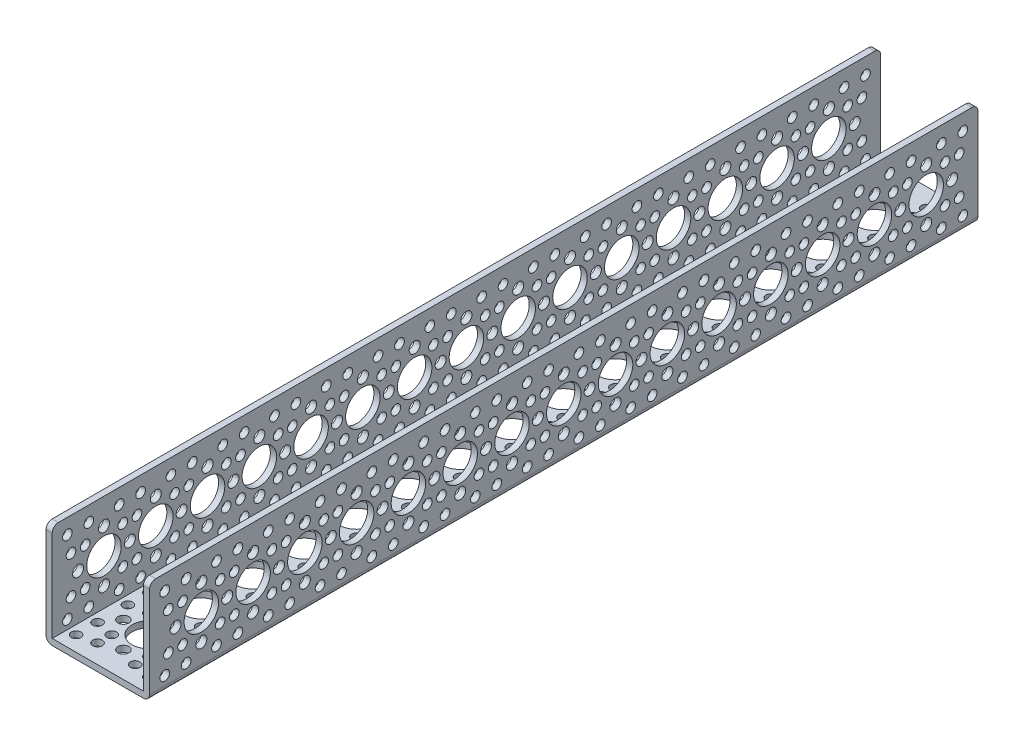
SolidWorks part; units mm, degrees
ref_plane "Front Plane" through (0, 0, 0) normal (0, 0, 1) x (1, 0, 0)
ref_plane "Top Plane" through (0, 0, 0) normal (0, 1, 0) x (1, 0, 0)
ref_plane "Right Plane" through (0, 0, 0) normal (1, 0, 0) x (0, 0, -1)
sketch "Sketch1" plane through (0, 0, 0) normal (0, 0, 1) x (1, 0, 0)
  line L1 (0, 0) -> (38.1, 0)
  line L2 (0, 0) -> (0, 38.1)
  line L4 (38.1, 0) -> (38.1, 38.1)
extrude "Extrude-Thin1" add sketch "Sketch1" along normal blind 304.8 thin thin type one direction wall 2.286
sketch "Sketch3" plane through (0, 0, 0) normal (0, -1, 0) x (1, 0, 0)
  line L0 (38.1, 0) -> (0, 0) construction
  circle B0 centre (19.05, 19.0584) radius 6.35
  circle B1 centre (19.05, 9.5334) radius 2.032
  circle B2 centre (9.525, 19.0584) radius 2.032
  circle B3 centre (19.05, 28.5834) radius 2.032
  circle B4 centre (28.575, 19.0584) radius 2.032
  circle B5 centre (12.1352, 25.9732) radius 1.778
  circle B6 centre (5.5796, 32.5288) radius 1.778
  circle B7 centre (25.9648, 25.9732) radius 1.778
  circle B8 centre (32.5204, 32.5288) radius 1.778
  circle B9 centre (25.9648, 12.1436) radius 1.778
  circle B10 centre (32.5204, 5.588) radius 1.778
  circle B11 centre (12.1352, 12.1436) radius 1.778
  circle B12 centre (5.5796, 5.588) radius 1.778
  circle B13 centre (12.1352, 31.1936) radius 1.778
  circle B14 centre (25.9648, 31.1936) radius 1.778
  circle B15 centre (25.9648, 6.9232) radius 1.778
  circle B16 centre (12.1352, 6.9232) radius 1.778
  circle B17 centre (32.5204, 13.4788) radius 1.778
  circle B18 centre (5.5796, 13.4788) radius 1.778
  circle B19 centre (5.5796, 24.638) radius 1.778
  circle B20 centre (32.5204, 24.638) radius 1.778
  circle B21 centre (18.9713, 38.1084) radius 6.35
  circle B22 centre (9.4463, 38.1084) radius 2.032
  circle B23 centre (28.4963, 38.1084) radius 2.032
  circle B24 centre (18.9713, 57.1584) radius 6.35
  circle B25 centre (18.9713, 47.6334) radius 2.032
  circle B26 centre (9.4463, 57.1584) radius 2.032
  circle B27 centre (18.9713, 66.6834) radius 2.032
  circle B28 centre (28.4963, 57.1584) radius 2.032
  circle B29 centre (12.0565, 64.0732) radius 1.778
  circle B30 centre (5.5009, 70.6288) radius 1.778
  circle B31 centre (25.8861, 64.0732) radius 1.778
  circle B32 centre (32.4417, 70.6288) radius 1.778
  circle B33 centre (25.8861, 50.2436) radius 1.778
  circle B34 centre (32.4417, 43.688) radius 1.778
  circle B35 centre (12.0565, 50.2436) radius 1.778
  circle B36 centre (5.5009, 43.688) radius 1.778
  circle B37 centre (12.0565, 69.2936) radius 1.778
  circle B38 centre (25.8861, 69.2936) radius 1.778
  circle B39 centre (25.8861, 45.0232) radius 1.778
  circle B40 centre (12.0565, 45.0232) radius 1.778
  circle B41 centre (32.4417, 51.5788) radius 1.778
  circle B42 centre (5.5009, 51.5788) radius 1.778
  circle B43 centre (5.5009, 62.738) radius 1.778
  circle B44 centre (32.4417, 62.738) radius 1.778
  circle B45 centre (18.9713, 76.2084) radius 6.35
  circle B46 centre (9.4463, 76.2084) radius 2.032
  circle B47 centre (28.4963, 76.2084) radius 2.032
  circle B48 centre (18.9713, 95.2584) radius 6.35
  circle B49 centre (18.9713, 85.7334) radius 2.032
  circle B50 centre (9.4463, 95.2584) radius 2.032
  circle B51 centre (18.9713, 104.7834) radius 2.032
  circle B52 centre (28.4963, 95.2584) radius 2.032
  circle B53 centre (12.0565, 102.1732) radius 1.778
  circle B54 centre (5.5009, 108.7288) radius 1.778
  circle B55 centre (25.8861, 102.1732) radius 1.778
  circle B56 centre (32.4417, 108.7288) radius 1.778
  circle B57 centre (25.8861, 88.3436) radius 1.778
  circle B58 centre (32.4417, 81.788) radius 1.778
  circle B59 centre (12.0565, 88.3436) radius 1.778
  circle B60 centre (5.5009, 81.788) radius 1.778
  circle B61 centre (12.0565, 107.3936) radius 1.778
  circle B62 centre (25.8861, 107.3936) radius 1.778
  circle B63 centre (25.8861, 83.1232) radius 1.778
  circle B64 centre (12.0565, 83.1232) radius 1.778
  circle B65 centre (32.4417, 89.6788) radius 1.778
  circle B66 centre (5.5009, 89.6788) radius 1.778
  circle B67 centre (5.5009, 100.838) radius 1.778
  circle B68 centre (32.4417, 100.838) radius 1.778
  circle B69 centre (18.9713, 133.3584) radius 6.35
  circle B70 centre (18.9713, 123.8334) radius 2.032
  circle B71 centre (9.4463, 133.3584) radius 2.032
  circle B72 centre (18.9713, 142.8834) radius 2.032
  circle B73 centre (28.4963, 133.3584) radius 2.032
  circle B74 centre (12.0565, 140.2732) radius 1.778
  circle B75 centre (5.5009, 146.8288) radius 1.778
  circle B76 centre (25.8861, 140.2732) radius 1.778
  circle B77 centre (32.4417, 146.8288) radius 1.778
  circle B78 centre (25.8861, 126.4436) radius 1.778
  circle B79 centre (32.4417, 119.888) radius 1.778
  circle B80 centre (12.0565, 126.4436) radius 1.778
  circle B81 centre (5.5009, 119.888) radius 1.778
  circle B82 centre (12.0565, 145.4936) radius 1.778
  circle B83 centre (25.8861, 145.4936) radius 1.778
  circle B84 centre (25.8861, 121.2232) radius 1.778
  circle B85 centre (12.0565, 121.2232) radius 1.778
  circle B86 centre (32.4417, 127.7788) radius 1.778
  circle B87 centre (5.5009, 127.7788) radius 1.778
  circle B88 centre (5.5009, 138.938) radius 1.778
  circle B89 centre (32.4417, 138.938) radius 1.778
  circle B90 centre (18.9713, 114.3084) radius 6.35
  circle B91 centre (9.4463, 114.3084) radius 2.032
  circle B92 centre (28.4963, 114.3084) radius 2.032
  circle B93 centre (18.9713, 152.4084) radius 6.35
  circle B94 centre (9.4463, 152.4084) radius 2.032
  circle B95 centre (28.4963, 152.4084) radius 2.032
  circle B96 centre (18.9713, 171.4584) radius 6.35
  circle B97 centre (18.9713, 161.9334) radius 2.032
  circle B98 centre (9.4463, 171.4584) radius 2.032
  circle B99 centre (18.9713, 180.9834) radius 2.032
  circle B100 centre (28.4963, 171.4584) radius 2.032
  circle B101 centre (12.0565, 178.3732) radius 1.778
  circle B102 centre (5.5009, 184.9288) radius 1.778
  circle B103 centre (25.8861, 178.3732) radius 1.778
  circle B104 centre (32.4417, 184.9288) radius 1.778
  circle B105 centre (25.8861, 164.5436) radius 1.778
  circle B106 centre (32.4417, 157.988) radius 1.778
  circle B107 centre (12.0565, 164.5436) radius 1.778
  circle B108 centre (5.5009, 157.988) radius 1.778
  circle B109 centre (12.0565, 183.5936) radius 1.778
  circle B110 centre (25.8861, 183.5936) radius 1.778
  circle B111 centre (25.8861, 159.3232) radius 1.778
  circle B112 centre (12.0565, 159.3232) radius 1.778
  circle B113 centre (32.4417, 165.8788) radius 1.778
  circle B114 centre (5.5009, 165.8788) radius 1.778
  circle B115 centre (5.5009, 177.038) radius 1.778
  circle B116 centre (32.4417, 177.038) radius 1.778
  circle B117 centre (18.9713, 209.5584) radius 6.35
  circle B118 centre (18.9713, 200.0334) radius 2.032
  circle B119 centre (9.4463, 209.5584) radius 2.032
  circle B120 centre (18.9713, 219.0834) radius 2.032
  circle B121 centre (28.4963, 209.5584) radius 2.032
  circle B122 centre (12.0565, 216.4732) radius 1.778
  circle B123 centre (5.5009, 223.0288) radius 1.778
  circle B124 centre (25.8861, 216.4732) radius 1.778
  circle B125 centre (32.4417, 223.0288) radius 1.778
  circle B126 centre (25.8861, 202.6436) radius 1.778
  circle B127 centre (32.4417, 196.088) radius 1.778
  circle B128 centre (12.0565, 202.6436) radius 1.778
  circle B129 centre (5.5009, 196.088) radius 1.778
  circle B130 centre (12.0565, 221.6936) radius 1.778
  circle B131 centre (25.8861, 221.6936) radius 1.778
  circle B132 centre (25.8861, 197.4232) radius 1.778
  circle B133 centre (12.0565, 197.4232) radius 1.778
  circle B134 centre (32.4417, 203.9788) radius 1.778
  circle B135 centre (5.5009, 203.9788) radius 1.778
  circle B136 centre (5.5009, 215.138) radius 1.778
  circle B137 centre (32.4417, 215.138) radius 1.778
  circle B138 centre (18.9713, 190.5084) radius 6.35
  circle B139 centre (9.4463, 190.5084) radius 2.032
  circle B140 centre (28.4963, 190.5084) radius 2.032
  circle B141 centre (18.9713, 228.6084) radius 6.35
  circle B142 centre (9.4463, 228.6084) radius 2.032
  circle B143 centre (28.4963, 228.6084) radius 2.032
  circle B144 centre (18.9713, 285.7584) radius 6.35
  circle B145 centre (18.9713, 276.2334) radius 2.032
  circle B146 centre (9.4463, 285.7584) radius 2.032
  circle B147 centre (18.9713, 295.2834) radius 2.032
  circle B148 centre (28.4963, 285.7584) radius 2.032
  circle B149 centre (12.0565, 292.6732) radius 1.778
  circle B150 centre (5.5009, 299.2288) radius 1.778
  circle B151 centre (25.8861, 292.6732) radius 1.778
  circle B152 centre (32.4417, 299.2288) radius 1.778
  circle B153 centre (25.8861, 278.8436) radius 1.778
  circle B154 centre (32.4417, 272.288) radius 1.778
  circle B155 centre (12.0565, 278.8436) radius 1.778
  circle B156 centre (5.5009, 272.288) radius 1.778
  circle B157 centre (12.0565, 297.8936) radius 1.778
  circle B158 centre (25.8861, 297.8936) radius 1.778
  circle B159 centre (25.8861, 273.6232) radius 1.778
  circle B160 centre (12.0565, 273.6232) radius 1.778
  circle B161 centre (32.4417, 280.1788) radius 1.778
  circle B162 centre (5.5009, 280.1788) radius 1.778
  circle B163 centre (5.5009, 291.338) radius 1.778
  circle B164 centre (32.4417, 291.338) radius 1.778
  circle B165 centre (18.9713, 247.6584) radius 6.35
  circle B166 centre (18.9713, 238.1334) radius 2.032
  circle B167 centre (9.4463, 247.6584) radius 2.032
  circle B168 centre (18.9713, 257.1834) radius 2.032
  circle B169 centre (28.4963, 247.6584) radius 2.032
  circle B170 centre (12.0565, 254.5732) radius 1.778
  circle B171 centre (5.5009, 261.1288) radius 1.778
  circle B172 centre (25.8861, 254.5732) radius 1.778
  circle B173 centre (32.4417, 261.1288) radius 1.778
  circle B174 centre (25.8861, 240.7436) radius 1.778
  circle B175 centre (32.4417, 234.188) radius 1.778
  circle B176 centre (12.0565, 240.7436) radius 1.778
  circle B177 centre (5.5009, 234.188) radius 1.778
  circle B178 centre (12.0565, 259.7936) radius 1.778
  circle B179 centre (25.8861, 259.7936) radius 1.778
  circle B180 centre (25.8861, 235.5232) radius 1.778
  circle B181 centre (12.0565, 235.5232) radius 1.778
  circle B182 centre (32.4417, 242.0788) radius 1.778
  circle B183 centre (5.5009, 242.0788) radius 1.778
  circle B184 centre (5.5009, 253.238) radius 1.778
  circle B185 centre (32.4417, 253.238) radius 1.778
  circle B186 centre (18.9713, 266.7084) radius 6.35
  circle B187 centre (9.4463, 266.7084) radius 2.032
  circle B188 centre (28.4963, 266.7084) radius 2.032
  dimension "D1" = 19.05
  dimension "D2" = 38.1
  dimension "D3" = 5.588
  dimension "D4" = 19.05
  dimension "D5" = 38.1
sketch_block_instance "actobotics hole pattern-2"
sketch_block "actobotics hole pattern" parameters "D1"=12.7, "D3"=4.064, "D6"=3.556, "D7"=3.556, "D2"=9.525, "D4"=19.05, "D5"=9.779
sketch_block_instance "Actobotics hole pattern c-6"
sketch_block "Actobotics hole pattern c" parameters "D1"=12.7, "D4"=4.064, "D2"=19.05, "D3"=9.525
sketch_block_instance "actobotics hole pattern-1"
sketch_block_instance "Actobotics hole pattern c-9"
sketch_block_instance "actobotics hole pattern-9"
sketch_block_instance "actobotics hole pattern-11"
sketch_block_instance "Actobotics hole pattern c-11"
sketch_block_instance "Actobotics hole pattern c-12"
sketch_block_instance "actobotics hole pattern-12"
sketch_block_instance "actobotics hole pattern-13"
sketch_block_instance "Actobotics hole pattern c-13"
sketch_block_instance "Actobotics hole pattern c-16"
sketch_block_instance "actobotics hole pattern-16"
sketch_block_instance "actobotics hole pattern-17"
sketch_block_instance "Actobotics hole pattern c-17"
extrude "Cut-Extrude1" cut sketch "Sketch3" against normal up to next (2.286 mm away)
sketch "Sketch4" plane through (0, 0, 0) normal (-1, 0, 0) x (0, 0, 1)
  line L0 (0, 19.05) -> (304.8, 19.05) construction
  line L1 (0, 0) -> (0, 38.1) construction
  line L3 (304.8, 0) -> (304.8, 38.1) construction
  circle B0 centre (266.7, 19.05) radius 6.35
  circle B1 centre (266.7, 9.525) radius 2.032
  circle B2 centre (266.7, 28.575) radius 2.032
  circle B3 centre (247.65, 19.05) radius 6.35
  circle B4 centre (257.175, 19.0494) radius 2.032
  circle B5 centre (247.6494, 9.525) radius 2.032
  circle B6 centre (238.125, 19.0506) radius 2.032
  circle B7 centre (247.6506, 28.575) radius 2.032
  circle B8 centre (240.7348, 12.1356) radius 1.778
  circle B9 centre (234.1788, 5.5804) radius 1.778
  circle B10 centre (240.7356, 25.9652) radius 1.778
  circle B11 centre (234.1804, 32.5212) radius 1.778
  circle B12 centre (254.5652, 25.9644) radius 1.778
  circle B13 centre (261.1212, 32.5196) radius 1.778
  circle B14 centre (254.5644, 12.1348) radius 1.778
  circle B15 centre (261.1196, 5.5788) radius 1.778
  circle B16 centre (235.5144, 12.1359) radius 1.778
  circle B17 centre (235.5152, 25.9655) radius 1.778
  circle B18 centre (259.7856, 25.9641) radius 1.778
  circle B19 centre (259.7848, 12.1345) radius 1.778
  circle B20 centre (253.2304, 32.5201) radius 1.778
  circle B21 centre (253.2288, 5.5793) radius 1.778
  circle B22 centre (242.0696, 5.5799) radius 1.778
  circle B23 centre (242.0712, 32.5207) radius 1.778
  circle B24 centre (285.75, 19.05) radius 6.35
  circle B25 centre (295.275, 19.05) radius 2.032
  circle B26 centre (285.75, 9.525) radius 2.032
  circle B27 centre (276.225, 19.05) radius 2.032
  circle B28 centre (285.75, 28.575) radius 2.032
  circle B29 centre (278.8352, 12.1352) radius 1.778
  circle B30 centre (272.2796, 5.5796) radius 1.778
  circle B31 centre (278.8352, 25.9648) radius 1.778
  circle B32 centre (272.2796, 32.5204) radius 1.778
  circle B33 centre (292.6648, 25.9648) radius 1.778
  circle B34 centre (299.2204, 32.5204) radius 1.778
  circle B35 centre (292.6648, 12.1352) radius 1.778
  circle B36 centre (299.2204, 5.5796) radius 1.778
  circle B37 centre (273.6148, 12.1352) radius 1.778
  circle B38 centre (273.6148, 25.9648) radius 1.778
  circle B39 centre (297.8852, 25.9648) radius 1.778
  circle B40 centre (297.8852, 12.1352) radius 1.778
  circle B41 centre (291.3296, 32.5204) radius 1.778
  circle B42 centre (291.3296, 5.5796) radius 1.778
  circle B43 centre (280.1704, 5.5796) radius 1.778
  circle B44 centre (280.1704, 32.5204) radius 1.778
  circle B45 centre (228.6002, 18.965) radius 6.35
  circle B46 centre (228.6002, 9.44) radius 2.032
  circle B47 centre (228.6002, 28.49) radius 2.032
  circle B48 centre (209.5506, 18.8391) radius 6.35
  circle B49 centre (219.0756, 18.8385) radius 2.032
  circle B50 centre (209.55, 9.3141) radius 2.032
  circle B51 centre (200.0256, 18.8396) radius 2.032
  circle B52 centre (209.5512, 28.3641) radius 2.032
  circle B53 centre (202.6354, 11.9247) radius 1.778
  circle B54 centre (196.0794, 5.3695) radius 1.778
  circle B55 centre (202.6362, 25.7543) radius 1.778
  circle B56 centre (196.081, 32.3103) radius 1.778
  circle B57 centre (216.4658, 25.7534) radius 1.778
  circle B58 centre (223.0218, 32.3086) radius 1.778
  circle B59 centre (216.465, 11.9239) radius 1.778
  circle B60 centre (223.0202, 5.3679) radius 1.778
  circle B61 centre (197.415, 11.925) radius 1.778
  circle B62 centre (197.4158, 25.7546) radius 1.778
  circle B63 centre (221.6862, 25.7531) radius 1.778
  circle B64 centre (221.6854, 11.9235) radius 1.778
  circle B65 centre (215.131, 32.3091) radius 1.778
  circle B66 centre (215.1294, 5.3683) radius 1.778
  circle B67 centre (203.9702, 5.369) radius 1.778
  circle B68 centre (203.9718, 32.3098) radius 1.778
  circle B69 centre (38.1006, 18.7951) radius 6.35
  circle B70 centre (38.1006, 9.2701) radius 2.032
  circle B71 centre (38.1006, 28.3201) radius 2.032
  circle B72 centre (19.0508, 18.7101) radius 6.35
  circle B73 centre (28.5758, 18.7096) radius 2.032
  circle B74 centre (19.0502, 9.1851) radius 2.032
  circle B75 centre (9.5258, 18.7107) radius 2.032
  circle B76 centre (19.0513, 28.2351) radius 2.032
  circle B77 centre (12.1355, 11.7957) radius 1.778
  circle B78 centre (5.5796, 5.2406) radius 1.778
  circle B79 centre (12.1364, 25.6253) radius 1.778
  circle B80 centre (5.5812, 32.1813) radius 1.778
  circle B81 centre (25.966, 25.6245) radius 1.778
  circle B82 centre (32.5219, 32.1797) radius 1.778
  circle B83 centre (25.9651, 11.7949) radius 1.778
  circle B84 centre (32.5203, 5.2389) radius 1.778
  circle B85 centre (6.9151, 11.7961) radius 1.778
  circle B86 centre (6.916, 25.6257) radius 1.778
  circle B87 centre (31.1864, 25.6242) radius 1.778
  circle B88 centre (31.1855, 11.7946) radius 1.778
  circle B89 centre (24.6312, 32.1802) radius 1.778
  circle B90 centre (24.6296, 5.2394) radius 1.778
  circle B91 centre (13.4703, 5.2401) radius 1.778
  circle B92 centre (13.4719, 32.1808) radius 1.778
  circle B93 centre (114.3005, 18.8641) radius 6.35
  circle B94 centre (114.3005, 9.3391) radius 2.032
  circle B95 centre (114.3005, 28.3891) radius 2.032
  circle B96 centre (76.2006, 18.7792) radius 6.35
  circle B97 centre (76.2006, 9.2542) radius 2.032
  circle B98 centre (76.2006, 28.3042) radius 2.032
  circle B99 centre (95.2505, 18.8641) radius 6.35
  circle B100 centre (104.7755, 18.8635) radius 2.032
  circle B101 centre (95.2499, 9.3391) radius 2.032
  circle B102 centre (85.7255, 18.8647) radius 2.032
  circle B103 centre (95.251, 28.3891) radius 2.032
  circle B104 centre (88.3352, 11.9497) radius 1.778
  circle B105 centre (81.7793, 5.3945) radius 1.778
  circle B106 centre (88.3361, 25.7793) radius 1.778
  circle B107 centre (81.7809, 32.3353) radius 1.778
  circle B108 centre (102.1657, 25.7785) radius 1.778
  circle B109 centre (108.7216, 32.3337) radius 1.778
  circle B110 centre (102.1648, 11.9489) radius 1.778
  circle B111 centre (108.72, 5.3929) radius 1.778
  circle B112 centre (83.1148, 11.95) radius 1.778
  circle B113 centre (83.1157, 25.7796) radius 1.778
  circle B114 centre (107.3861, 25.7782) radius 1.778
  circle B115 centre (107.3852, 11.9486) radius 1.778
  circle B116 centre (100.8309, 32.3342) radius 1.778
  circle B117 centre (100.8293, 5.3934) radius 1.778
  circle B118 centre (89.67, 5.3941) radius 1.778
  circle B119 centre (89.6716, 32.3348) radius 1.778
  circle B120 centre (57.1509, 18.6782) radius 6.35
  circle B121 centre (66.6759, 18.6777) radius 2.032
  circle B122 centre (57.1503, 9.1532) radius 2.032
  circle B123 centre (47.6259, 18.6788) radius 2.032
  circle B124 centre (57.1515, 28.2032) radius 2.032
  circle B125 centre (50.2357, 11.7639) radius 1.778
  circle B126 centre (43.6797, 5.2087) radius 1.778
  circle B127 centre (50.2365, 25.5934) radius 1.778
  circle B128 centre (43.6813, 32.1494) radius 1.778
  circle B129 centre (64.0661, 25.5926) radius 1.778
  circle B130 centre (70.6221, 32.1478) radius 1.778
  circle B131 centre (64.0653, 11.763) radius 1.778
  circle B132 centre (70.6205, 5.207) radius 1.778
  circle B133 centre (45.0153, 11.7642) radius 1.778
  circle B134 centre (45.0161, 25.5938) radius 1.778
  circle B135 centre (69.2865, 25.5923) radius 1.778
  circle B136 centre (69.2857, 11.7627) radius 1.778
  circle B137 centre (62.7313, 32.1483) radius 1.778
  circle B138 centre (62.7297, 5.2075) radius 1.778
  circle B139 centre (51.5705, 5.2082) radius 1.778
  circle B140 centre (51.5721, 32.149) radius 1.778
  circle B141 centre (171.4506, 18.8391) radius 6.35
  circle B142 centre (180.9756, 18.8385) radius 2.032
  circle B143 centre (171.45, 9.3141) radius 2.032
  circle B144 centre (161.9256, 18.8396) radius 2.032
  circle B145 centre (171.4512, 28.3641) radius 2.032
  circle B146 centre (164.5354, 11.9247) radius 1.778
  circle B147 centre (157.9794, 5.3695) radius 1.778
  circle B148 centre (164.5362, 25.7543) radius 1.778
  circle B149 centre (157.981, 32.3103) radius 1.778
  circle B150 centre (178.3658, 25.7534) radius 1.778
  circle B151 centre (184.9218, 32.3086) radius 1.778
  circle B152 centre (178.365, 11.9239) radius 1.778
  circle B153 centre (184.9202, 5.3679) radius 1.778
  circle B154 centre (159.315, 11.925) radius 1.778
  circle B155 centre (159.3158, 25.7546) radius 1.778
  circle B156 centre (183.5862, 25.7531) radius 1.778
  circle B157 centre (183.5854, 11.9235) radius 1.778
  circle B158 centre (177.031, 32.3091) radius 1.778
  circle B159 centre (177.0294, 5.3683) radius 1.778
  circle B160 centre (165.8702, 5.369) radius 1.778
  circle B161 centre (165.8718, 32.3098) radius 1.778
  circle B162 centre (133.3512, 18.6281) radius 6.35
  circle B163 centre (142.8762, 18.6276) radius 2.032
  circle B164 centre (133.3506, 9.1031) radius 2.032
  circle B165 centre (123.8262, 18.6287) radius 2.032
  circle B166 centre (133.3517, 28.1531) radius 2.032
  circle B167 centre (126.436, 11.7137) radius 1.778
  circle B168 centre (119.88, 5.1585) radius 1.778
  circle B169 centre (126.4368, 25.5433) radius 1.778
  circle B170 centre (119.8816, 32.0993) radius 1.778
  circle B171 centre (140.2664, 25.5425) radius 1.778
  circle B172 centre (146.8224, 32.0977) radius 1.778
  circle B173 centre (140.2656, 11.7129) radius 1.778
  circle B174 centre (146.8207, 5.1569) radius 1.778
  circle B175 centre (121.2156, 11.7141) radius 1.778
  circle B176 centre (121.2164, 25.5437) radius 1.778
  circle B177 centre (145.4868, 25.5422) radius 1.778
  circle B178 centre (145.486, 11.7126) radius 1.778
  circle B179 centre (138.9316, 32.0982) radius 1.778
  circle B180 centre (138.93, 5.1574) radius 1.778
  circle B181 centre (127.7707, 5.1581) radius 1.778
  circle B182 centre (127.7724, 32.0988) radius 1.778
  circle B183 centre (152.4008, 18.7541) radius 6.35
  circle B184 centre (152.4008, 9.2291) radius 2.032
  circle B185 centre (152.4008, 28.2791) radius 2.032
  circle B186 centre (190.5006, 18.8391) radius 6.35
  circle B187 centre (190.5006, 9.3141) radius 2.032
  circle B188 centre (190.5006, 28.3641) radius 2.032
  dimension "D1" = 19.05
  dimension "D2" = 38.1
  dimension "D3" = 5.5796
  dimension "D4" = 19.05
  dimension "D5" = 38.1
sketch_block_instance "Actobotics hole pattern c-7"
sketch_block_instance "actobotics hole pattern-6"
sketch_block_instance "actobotics hole pattern-7"
sketch_block_instance "Actobotics hole pattern c-8"
sketch_block_instance "actobotics hole pattern-8"
sketch_block_instance "Actobotics hole pattern c-10"
sketch_block_instance "actobotics hole pattern-10"
sketch_block_instance "Actobotics hole pattern c-14"
sketch_block_instance "Actobotics hole pattern c-15"
sketch_block_instance "actobotics hole pattern-14"
sketch_block_instance "actobotics hole pattern-15"
sketch_block_instance "actobotics hole pattern-18"
sketch_block_instance "actobotics hole pattern-19"
sketch_block_instance "Actobotics hole pattern c-18"
sketch_block_instance "Actobotics hole pattern c-19"
extrude "Cut-Extrude2" cut sketch "Sketch4" against normal through all
fillet "Fillet1" radius 2.286 6 edges at (1.143, 38.1, 304.8) (36.957, 38.1, 304.8) (36.957, 38.1, 0) (1.143, 38.1, 0) (38.1, 0, 152.4) (0, 0, 152.4)
